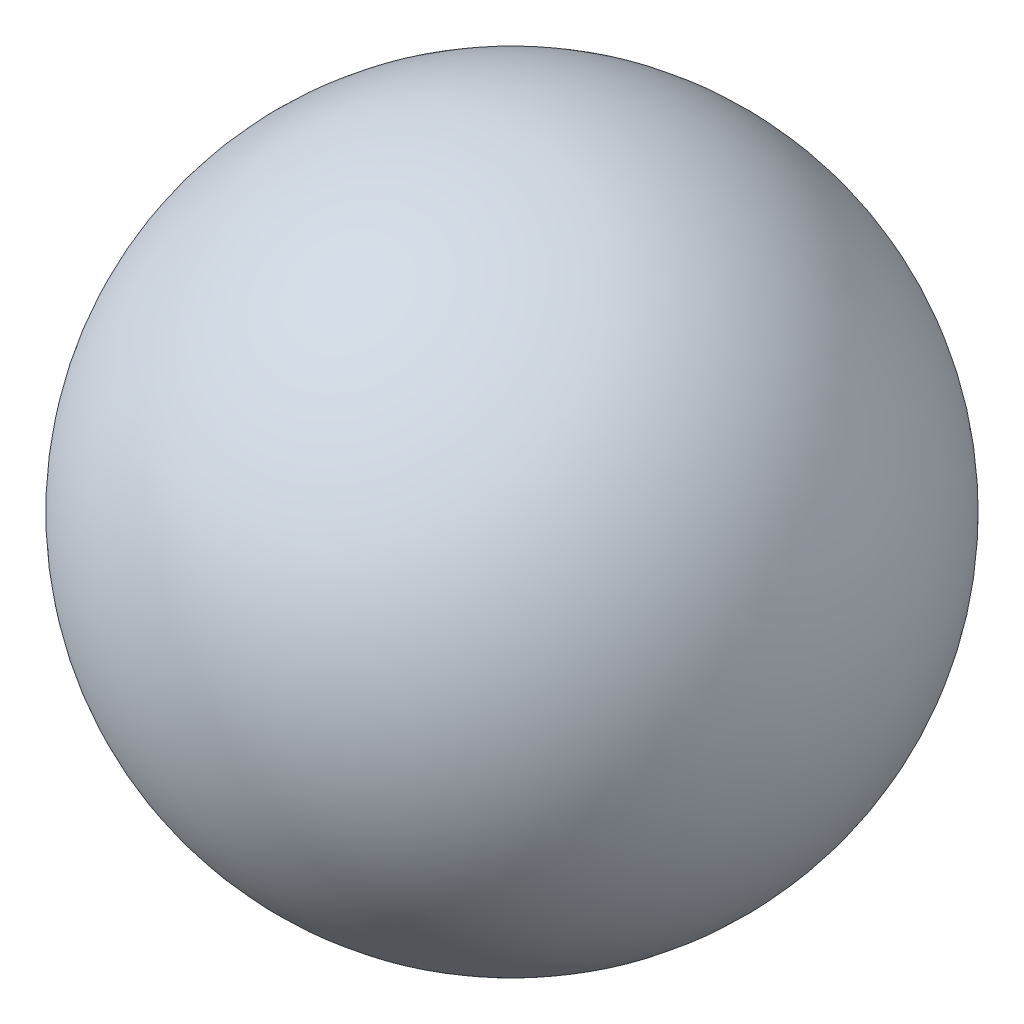
SolidWorks part; units mm, degrees
ref_plane "Front Plane" through (0, 0, 0) normal (0, 0, 1) x (1, 0, 0)
ref_plane "Top Plane" through (0, 0, 0) normal (0, 1, 0) x (1, 0, 0)
ref_plane "Right Plane" through (0, 0, 0) normal (1, 0, 0) x (0, 0, -1)
sketch "Sketch1" plane through (0, 0, 0) normal (0, 0, 1) x (1, 0, 0)
  line L0 (0, 0) -> (0, 76)
  line L1 (0, 0) -> (0, -76)
  arc A0 (0, 76) -> (0, -76) centre (0, 0) ccw
  dimension "D1" = 152
revolve "Revolve3" add sketch "Sketch1" angle 360 about L0
